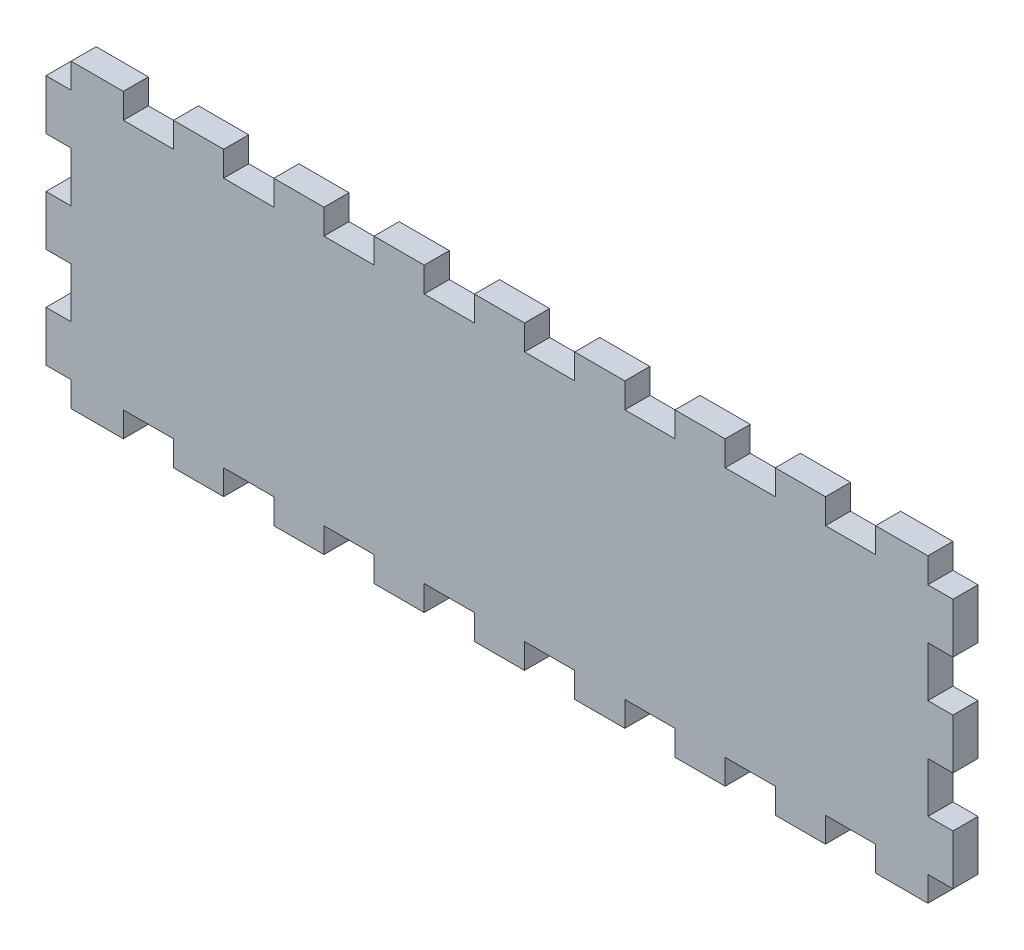
SolidWorks part; units mm, degrees
ref_plane "Front Plane" through (0, 0, 0) normal (0, 0, 1) x (1, 0, 0)
ref_plane "Top Plane" through (0, 0, 0) normal (0, 1, 0) x (1, 0, 0)
ref_plane "Right Plane" through (0, 0, 0) normal (1, 0, 0) x (0, 0, -1)
sketch "Sketch2" plane through (0, 0, 0) normal (0, 0, 1) x (1, 0, 0)
  line L0 (-78, 6) -> (-78, 0)
  line L1 (-78, 0) -> (-90, 0)
  line L2 (-90, 0) -> (-90, 6)
  line L3 (-90, 6) -> (-102.5, 6)
  line L4 (-102.5, 6) -> (-102.5, 0)
  line L5 (-78, 6) -> (-66, 6)
  line L6 (-66, 6) -> (-66, 0)
  line L7 (-66, 0) -> (-54, 0)
  line L8 (-54, 0) -> (-54, 6)
  line L9 (-54, 6) -> (-42, 6)
  line L10 (-42, 6) -> (-42, 0)
  line L11 (-42, 0) -> (-30, 0)
  line L12 (-30, 0) -> (-30, 6)
  line L13 (-30, 6) -> (-18, 6)
  line L14 (-18, 6) -> (-18, 0)
  line L15 (-18, 0) -> (-6, 0)
  line L16 (-6, 0) -> (6, 0) construction
  line L17 (-6, 0) -> (-6, 6) construction
  line L18 (-6, 0) -> (-6, 6)
  line L19 (-6, 6) -> (6, 6)
  line L20 (6, 6) -> (6, 0)
  line L21 (6, 0) -> (18, 0)
  line L22 (18, 0) -> (18, 6)
  line L23 (18, 6) -> (30, 6)
  line L24 (30, 6) -> (30, 0)
  line L25 (30, 0) -> (42, 0)
  line L26 (42, 0) -> (42, 6) construction
  line L27 (42, 0) -> (42, 6)
  line L28 (42, 6) -> (54, 6) construction
  line L29 (42, 6) -> (54, 6)
  line L30 (54, 6) -> (54, 0)
  line L31 (54, 0) -> (66, 0)
  line L32 (66, 0) -> (66, 6) construction
  line L33 (66, 0) -> (66, 6)
  line L34 (66, 6) -> (78, 6)
  line L35 (78, 6) -> (78, 0)
  line L36 (78, 0) -> (90, 0)
  line L37 (90, 0) -> (90, 6) construction
  line L38 (90, 0) -> (90, 6)
  line L39 (90, 6) -> (102.5, 6) construction
  line L40 (90, 6) -> (102.5, 6)
  line L41 (102.5, 6) -> (102.5, 0) construction
  line L42 (102.5, 6) -> (102.5, 0)
  line L43 (90, 0) -> (102.5, 0) construction
  line L44 (-102.5, 0) -> (-102.5, -59.9994)
  line L45 (-102.5, -29.9997) -> (102.5, -29.9997)
  line L46 (102.5, -65.9994) -> (102.5, -59.9994)
  line L47 (90, -65.9994) -> (102.5, -65.9994)
  line L48 (90, -59.9994) -> (90, -65.9994)
  line L49 (78, -59.9994) -> (90, -59.9994)
  line L50 (78, -65.9994) -> (78, -59.9994)
  line L51 (66, -65.9994) -> (78, -65.9994)
  line L52 (66, -59.9994) -> (66, -65.9994)
  line L53 (54, -59.9994) -> (66, -59.9994)
  line L54 (54, -65.9994) -> (54, -59.9994)
  line L55 (42, -65.9994) -> (54, -65.9994)
  line L56 (42, -59.9994) -> (42, -65.9994)
  line L57 (30, -59.9994) -> (42, -59.9994)
  line L58 (30, -65.9994) -> (30, -59.9994)
  line L59 (18, -65.9994) -> (30, -65.9994)
  line L60 (18, -59.9994) -> (18, -65.9994)
  line L61 (6, -59.9994) -> (18, -59.9994)
  line L62 (6, -65.9994) -> (6, -59.9994)
  line L63 (-6, -65.9994) -> (6, -65.9994)
  line L64 (-6, -59.9994) -> (-6, -65.9994)
  line L65 (-18, -59.9994) -> (-6, -59.9994)
  line L66 (-18, -65.9994) -> (-18, -59.9994)
  line L67 (-30, -65.9994) -> (-18, -65.9994)
  line L68 (-30, -59.9994) -> (-30, -65.9994)
  line L69 (-42, -59.9994) -> (-30, -59.9994)
  line L70 (-42, -65.9994) -> (-42, -59.9994)
  line L71 (-54, -65.9994) -> (-42, -65.9994)
  line L72 (-54, -59.9994) -> (-54, -65.9994)
  line L73 (-66, -59.9994) -> (-54, -59.9994)
  line L74 (-66, -65.9994) -> (-66, -59.9994)
  line L75 (-78, -65.9994) -> (-66, -65.9994)
  line L76 (-102.5, -65.9994) -> (-102.5, -59.9994)
  line L77 (-90, -65.9994) -> (-102.5, -65.9994)
  line L78 (-90, -59.9994) -> (-90, -65.9994)
  line L79 (-78, -59.9994) -> (-90, -59.9994)
  line L80 (-78, -65.9994) -> (-78, -59.9994)
  line L82 (102.5, 0) -> (102.5, -59.9994)
  point P116 (0, 0)
  point P117 (102.5, -29.9997)
  line M11 (-78, 0) -> (-66, 0)
  dimension "D1" = 59.9994
extrude "Boss-Extrude1" add sketch "Sketch2" along normal blind 6 contours L82 L42 L40 L38 L36 L35 L34 L33 L31 L30 L29 L27 L25 L24 L23 L22 L21 L20 L19 L18 L15 L14 L13 L12 L11 L10 L9 L8 L7 L1 L2 L3 L4 L44 L45 M11
sketch "Sketch3" plane through (0, 0, 6) normal (0, 0, 1) x (1, 0, 0)
  line L0 (-102.5, 6) -> (-102.5, -65.9994) construction
  line L1 (-102.5, 0) -> (-108.5, 0)
  line L2 (-102.5, 0) -> (-102.5, -12)
  line L3 (-102.5, -12) -> (-108.5, -12)
  line L4 (-108.5, 0) -> (-108.5, -12)
  line L5 (-90, 6) -> (-102.5, 6) construction
  line L6 (108.5, 0) -> (108.5, -12)
  line L7 (108.5, 0) -> (102.5, 0)
  line L8 (102.5, 0) -> (102.5, -12)
  line L9 (108.5, -12) -> (102.5, -12)
  line L10 (108.5, -24) -> (108.5, -36)
  line L11 (108.5, -24) -> (102.5, -24)
  line L12 (102.5, -24) -> (102.5, -36)
  line L13 (108.5, -36) -> (102.5, -36)
  line L14 (108.5, -48) -> (108.5, -60)
  line L15 (108.5, -48) -> (102.5, -48)
  line L16 (102.5, -48) -> (102.5, -60)
  line L17 (108.5, -60) -> (102.5, -60)
  line L18 (-102.5, -24) -> (-102.5, -36)
  line L19 (-102.5, -24) -> (-108.5, -24)
  line L20 (-108.5, -24) -> (-108.5, -36)
  line L21 (-102.5, -36) -> (-108.5, -36)
  line L22 (-102.5, -48) -> (-102.5, -60)
  line L23 (-102.5, -48) -> (-108.5, -48)
  line L24 (-108.5, -48) -> (-108.5, -60)
  line L25 (-102.5, -60) -> (-108.5, -60)
  line L26 (102.5, 6) -> (102.5, -65.9994) construction
  line L27 (102.5, -24) -> (102.5, -12) construction
  line L28 (102.5, -48) -> (102.5, -36) construction
  point P8 (0, 0)
  point P31 (0, 0)
  point P32 (0, 0)
  point P35 (0, 0)
  point P36 (0, 0)
  dimension "D1" = 12
  dimension "D2" = 6
  dimension "D3" = 6
  dimension "D6" = 12
  dimension "D4" = 2
  dimension "D5" = 3
extrude "Boss-Extrude2" add sketch "Sketch3" against normal blind 6
